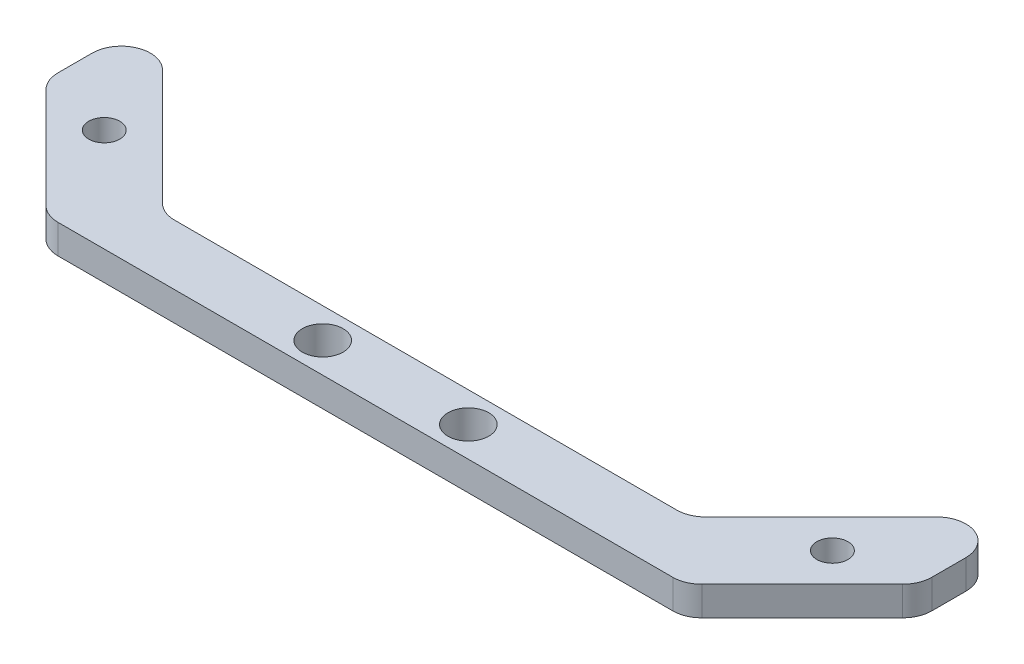
SolidWorks part; units mm, degrees
material "Carbon Fiber"
ref_plane "Front Plane" through (0, 0, 0) normal (0, 0, 1) x (1, 0, 0)
ref_plane "Top Plane" through (0, 0, 0) normal (0, 1, 0) x (1, 0, 0)
ref_plane "Right Plane" through (0, 0, 0) normal (1, 0, 0) x (0, 0, -1)
sketch "Sketch1" plane through (0, 0, 0) normal (0, 1, 0) x (1, 0, 0)
  line L0 (0, 6) -> (15, -9) construction
  line L2 (0, 0) -> (0, 12)
  line L4 (90, 0) -> (90, 12)
  line L5 (45, -3) -> (45, -15) construction
  line L6 (0, 12) -> (15, -3)
  line L7 (15, -3) -> (75, -3)
  line L8 (75, -3) -> (90, 12)
  line L9 (0, 0) -> (15, -15)
  line L10 (15, -15) -> (75, -15)
  line L11 (75, -15) -> (90, 0)
  line L12 (15, -9) -> (75, -9) construction
  line L13 (75, -9) -> (90, 6) construction
  line L14 (15, -3) -> (15, -9) construction
  line L15 (15, -9) -> (15, -15) construction
  line L16 (75, -3) -> (75, -9) construction
  line L17 (75, -9) -> (75, -15) construction
  circle A0 centre (7.5, -1.5) radius 1.6
  circle A2 centre (37.5, -9) radius 2.1
  circle A3 centre (82.5, -1.5) radius 1.6
  circle A4 centre (52.5, -9) radius 2.1
  point P23 (0, 0)
  dimension "D3" = 7.5
  dimension "D4" = 7.5
  dimension "D5" = 4.2
  dimension "D6" = 3.2
  dimension "D1" = 90
  dimension "D2" = 12
  dimension "D7" = 15
  dimension "D8" = 15
extrude "Boss-Extrude1" add sketch "Sketch1" along normal blind 3
sketch "Sketch2" plane through (0, 3, 0) normal (0, 1, 0) x (1, 0, 0)
  line L0 (15, -3) -> (17.9, -5.9)
  line L1 (17.9, -5.9) -> (72.1, -5.9)
  line L2 (72.1, -5.9) -> (75, -3)
  line L3 (90, 12) -> (75, -3) construction
  line L4 (75, -3) -> (15, -3) construction
  line L5 (75, -3) -> (15, -3)
  line L6 (12.1, -12.1) -> (77.9, -12.1)
  line L7 (0, 0) -> (15, -15) construction
  line L8 (75, -15) -> (90, 0) construction
  line L9 (77.9, -12.1) -> (75, -15)
  line L10 (75, -15) -> (15, -15)
  line L11 (15, -15) -> (12.1, -12.1)
  line L12 (15, -3) -> (0, 12) construction
  circle A0 centre (37.5, -9) radius 2.1 construction
  dimension "D1" = 1
  dimension "D2" = 1
extrude "Cut-Extrude1" cut sketch "Sketch2" against normal through all
fillet "Fillet1" radius 3 8 edges at (0, 1.5, 0) (90, 1.5, -12) (90, 1.5, 0) (0, 1.5, -12) (17.9, 1.5, 5.9) (77.9, 1.5, 12.1) (72.1, 1.5, 5.9) (12.1, 1.5, 12.1)
